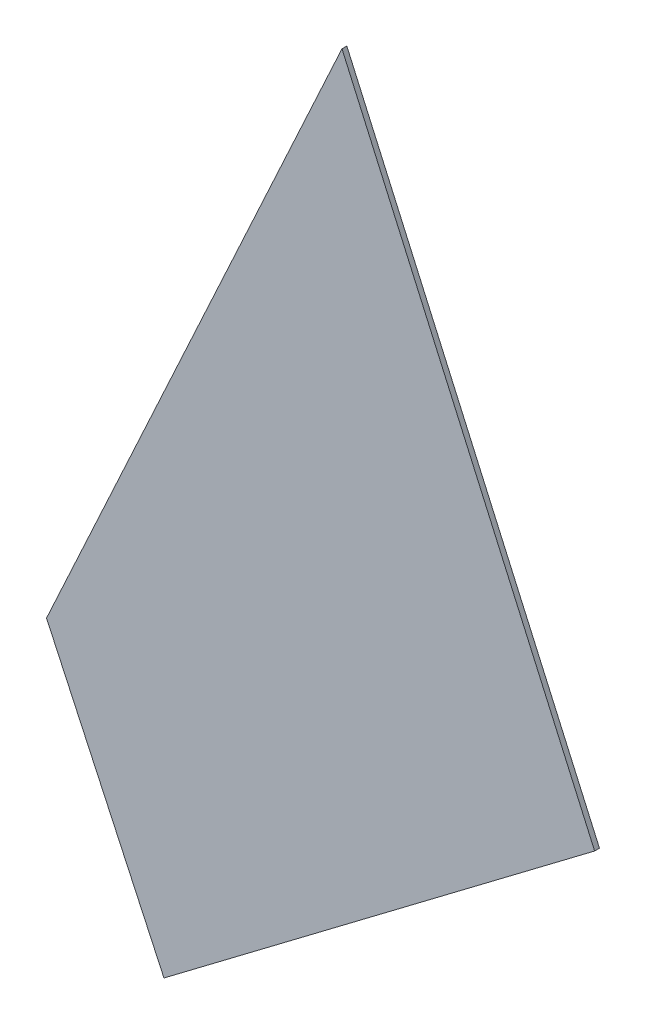
SolidWorks part; units mm, degrees
ref_plane "Alzado" through (0, 0, 0) normal (0, 0, 1) x (1, 0, 0)
ref_plane "Planta" through (0, 0, 0) normal (0, 1, 0) x (1, 0, 0)
ref_plane "Vista lateral" through (0, 0, 0) normal (1, 0, 0) x (0, 0, -1)
sketch "Model" plane through (0, 0, 0) normal (0, 0, 1) x (1, 0, 0)
  line L0 (51.1613, 15.5555) -> (45.9389, 27.3045)
  line L1 (42.2595, 8.8319) -> (39.8319, 14.0606)
  line L2 (39.8319, 14.0606) -> (45.9389, 27.3045)
  line L3 (51.1613, 15.5555) -> (42.2595, 8.8319)
extrude "Saliente-Extruir1" add sketch "Model" along normal blind 0.1
